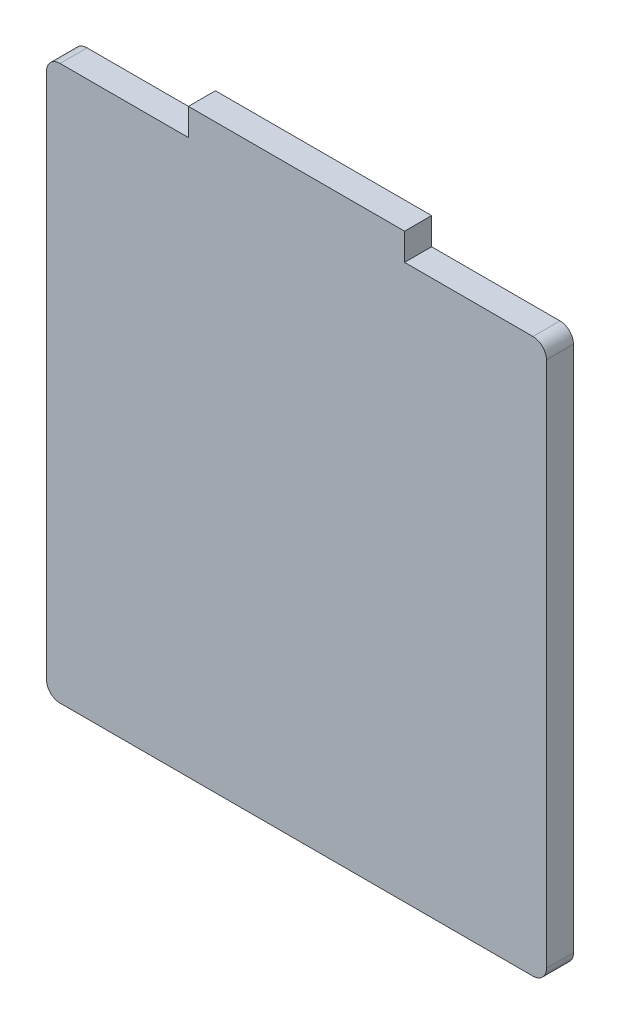
SolidWorks part; units mm, degrees
material "PLA"
ref_plane "Front Plane" through (0, 0, 0) normal (0, 0, 1) x (1, 0, 0)
ref_plane "Top Plane" through (0, 0, 0) normal (0, 1, 0) x (1, 0, 0)
ref_plane "Right Plane" through (0, 0, 0) normal (1, 0, 0) x (0, 0, -1)
sketch "Sketch2" plane through (0, 0, 0) normal (0, 0, 1) x (1, 0, 0)
  line L0 (25.4, 65.0875) -> (58.7375, 65.0875)
  line L1 (-58.7375, -65.0875) -> (58.7375, -65.0875)
  line L2 (-58.7375, -65.0875) -> (-58.7375, 65.0875)
  line L3 (-58.7375, 65.0875) -> (-25.4, 65.0875)
  line L4 (58.7375, -65.0875) -> (58.7375, 65.0875)
  line L5 (-58.7375, -65.0875) -> (58.7375, 65.0875) construction
  line L6 (-58.7375, 65.0875) -> (58.7375, -65.0875) construction
  line L8 (-25.4, 65.0875) -> (-25.4, 71.4375)
  line L9 (-25.4, 71.4375) -> (25.4, 71.4375)
  line L10 (25.4, 65.0875) -> (25.4, 71.4375)
  point P0 (0, 0)
  dimension "D1" = 117.475
  dimension "D2" = 130.175
  dimension "D3" = 50.8
  dimension "D4" = 6.35
extrude "Boss-Extrude1" add sketch "Sketch2" along normal blind 6.35 contours L3 L8 L9 L10 L0 L4 L1 L2
fillet "Fillet1" radius 3.175 4 edges at (-58.7375, -65.0875, 3.175) (58.7375, -65.0875, 3.175) (58.7375, 65.0875, 3.175) (-58.7375, 65.0875, 3.175)
equation "\"width\"= 5.5625in"
equation "\"height\"= 6.1875in"
equation "\"shell\"= 0.25in"
equation "\"extrude\"= 0.5in"
equation "\"D1@Boss-Extrude1\"=\"extrude\""
equation "\"D1@Shell1\"=\"shell\""
